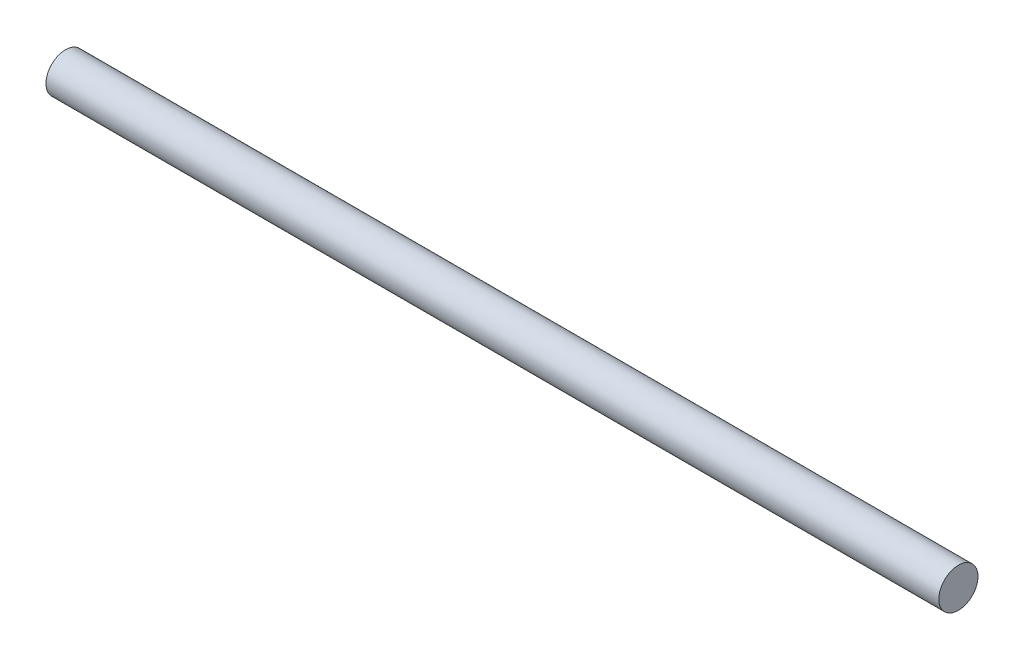
SolidWorks part; units mm, degrees
ref_plane "Front Plane" through (0, 0, 0) normal (0, 0, 1) x (1, 0, 0)
ref_plane "Top Plane" through (0, 0, 0) normal (0, 1, 0) x (1, 0, 0)
ref_plane "Right Plane" through (0, 0, 0) normal (1, 0, 0) x (0, 0, -1)
sketch "Sketch1" plane through (0, 0, 0) normal (1, 0, 0) x (0, 0, -1)
  circle A0 centre (0, 0) radius 3.9688
  dimension "D1" = 7.9375
extrude "Boss-Extrude1" add sketch "Sketch1" along normal mid plane 180.975
